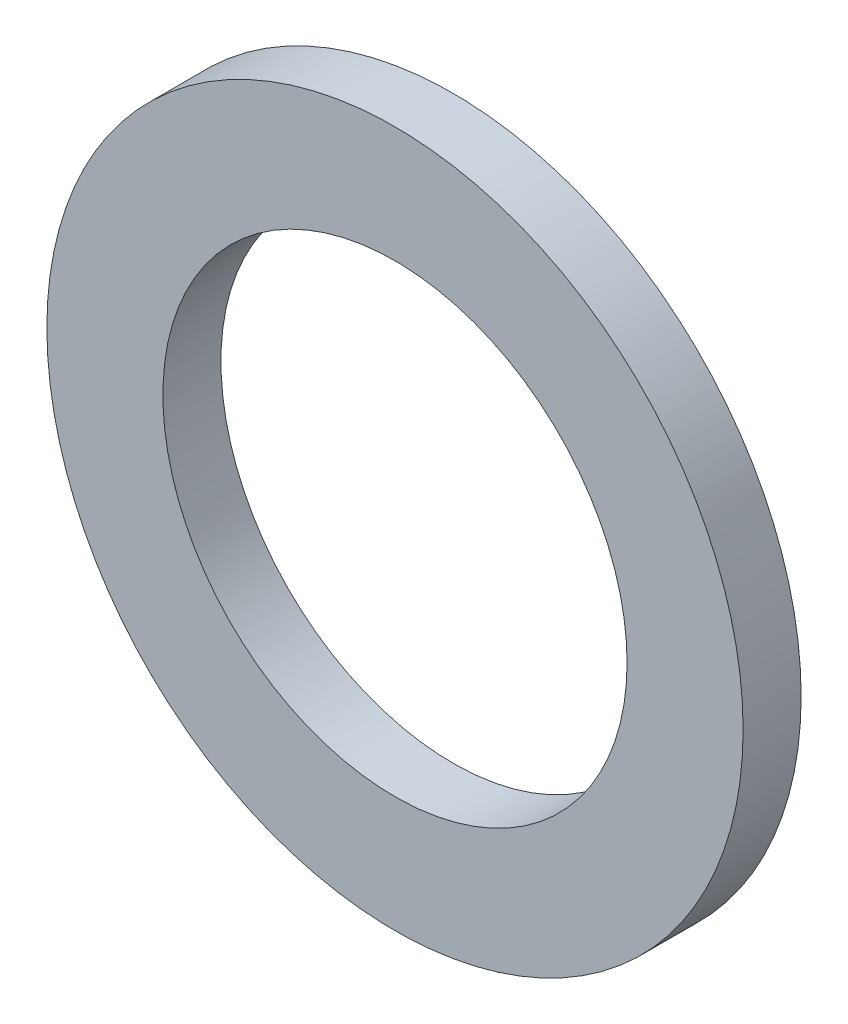
SolidWorks part; units mm, degrees
material "Тефлон"
ref_plane "Спереди" through (0, 0, 0) normal (0, 0, 1) x (1, 0, 0)
ref_plane "Сверху" through (0, 0, 0) normal (0, 1, 0) x (1, 0, 0)
ref_plane "Справа" through (0, 0, 0) normal (1, 0, 0) x (0, 0, -1)
sketch "Эскиз1" plane through (0, 0, 0) normal (0, 0, 1) x (1, 0, 0)
  circle A0 centre (0, 0) radius 9
  circle A1 centre (0, 0) radius 6
  dimension "D1" = 18
  dimension "D2" = 12
extrude "Бобышка-Вытянуть1" add sketch "Эскиз1" along normal blind 1.5
